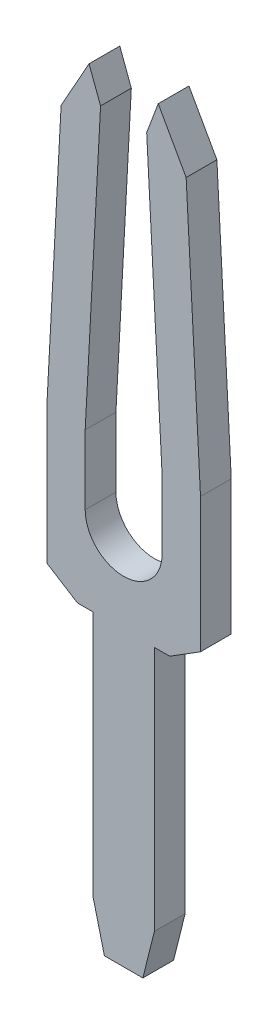
SolidWorks part; units mm, degrees
ref_plane "Front Plane" through (0, 0, 0) normal (0, 0, 1) x (1, 0, 0)
ref_plane "Top Plane" through (0, 0, 0) normal (0, 1, 0) x (1, 0, 0)
ref_plane "Right Plane" through (0, 0, 0) normal (1, 0, 0) x (0, 0, -1)
sketch "Szkic1" plane through (0, 0, 0) normal (0, 0, 1) x (1, 0, 0)
  line L0 (0.25, -4.975) -> (0.4, -4.375)
  line L1 (0.4, -4.375) -> (0.4, -1.175)
  line L2 (0.4, -1.175) -> (0.6, -1.175)
  line L3 (0.6, -1.175) -> (1, -0.925)
  line L4 (1, -0.925) -> (1, 0.825)
  line L5 (1, 0.825) -> (0.8133, 4.325)
  line L6 (0.8133, 4.325) -> (0.45, 4.975)
  line L7 (0.45, 4.975) -> (0.3, 4.575)
  line L8 (0.3, 4.575) -> (0.5, 0.825)
  line L9 (0.5, 0.825) -> (0.5, -0.075)
  line L10 (-0.5, -0.075) -> (-0.5, 0.825)
  line L11 (-0.5, 0.825) -> (-0.3, 4.575)
  line L12 (-0.3, 4.575) -> (-0.45, 4.975)
  line L13 (-0.45, 4.975) -> (-0.8133, 4.325)
  line L14 (-0.8133, 4.325) -> (-1, 0.825)
  line L15 (-1, 0.825) -> (-1, -0.925)
  line L16 (-1, -0.925) -> (-0.6, -1.175)
  line L17 (-0.6, -1.175) -> (-0.4, -1.175)
  line L18 (-0.4, -1.175) -> (-0.4, -4.375)
  line L19 (-0.4, -4.375) -> (-0.25, -4.975)
  line L20 (-0.25, -4.975) -> (0.25, -4.975)
  arc A0 (-0.5, -0.075) -> (0.5, -0.075) centre (0, -0.075) ccw
extrude "Dodanie-wyciągnięcie1" add sketch "Szkic1" along normal blind 0.4
